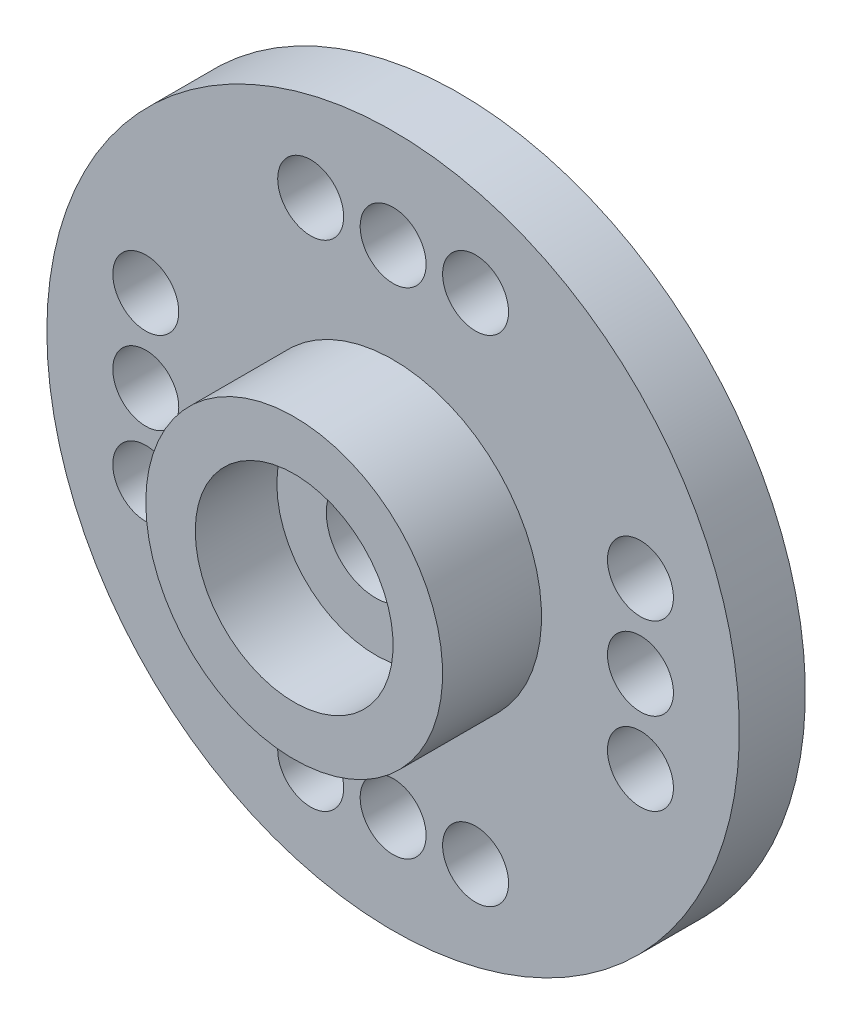
SolidWorks part; units mm, degrees
ref_plane "Alzado" through (0, 0, 0) normal (0, 0, 1) x (1, 0, 0)
ref_plane "Planta" through (0, 0, 0) normal (0, 1, 0) x (1, 0, 0)
ref_plane "Vista lateral" through (0, 0, 0) normal (1, 0, 0) x (0, 0, -1)
sketch "Croquis2" plane through (0, 0, 0) normal (1, 0, 0) x (0, 0, -1)
  line L0 (0, 0) -> (0, 1.5) construction
  line L1 (0, 1.5) -> (0, 3) construction
  line L2 (0, 3) -> (1.5, 3) construction
  line L3 (1.5, 3) -> (1.5, 3.5) construction
  line L4 (1.5, 3.5) -> (-0.5, 3.5) construction
  line L5 (-0.5, 3.5) -> (-0.5, 4.5) construction
  line L6 (-0.5, 4.5) -> (1, 4.5) construction
  line L7 (1, 4.5) -> (1, 10.5) construction
  line L8 (1, 10.5) -> (-1, 10.5) construction
  line L9 (-1, 10.5) -> (-1, 4.5) construction
  line L10 (-1, 4.5) -> (-4, 4.5) construction
  line L11 (-4, 4.5) -> (-4, 3) construction
  line L12 (-4, 3) -> (-1.5255, 3) construction
  line L13 (-1.5255, 3) -> (-1.5255, 1.5) construction
  line L14 (-1.5255, 1.5) -> (0, 1.5) construction
  line L15 (0, 1.5) -> (0, 3)
  line L16 (0, 3) -> (1.5, 3)
  line L17 (1.5, 3) -> (1.5, 3.5)
  line L18 (1.5, 3.5) -> (-0.5, 3.5)
  line L19 (-0.5, 3.5) -> (-0.5, 4.5)
  line L20 (-0.5, 4.5) -> (1, 4.5)
  line L21 (1, 4.5) -> (1, 10.5)
  line L22 (1, 10.5) -> (-1, 10.5)
  line L23 (-1, 10.5) -> (-1, 4.5)
  line L24 (-1, 4.5) -> (-4, 4.5)
  line L25 (-4, 4.5) -> (-4, 3)
  line L26 (-4, 3) -> (-1.5255, 3)
  line L27 (-1.5255, 3) -> (-1.5255, 1.5)
  line L28 (-1.5255, 1.5) -> (0, 1.5)
  line L29 (0, 0) -> (-7.3524, 0) construction
  dimension "D1" = 1.5
  dimension "D2" = 1.5
  dimension "D3" = 0.5
  dimension "D6" = 6
  dimension "D7" = 1
  dimension "D8" = 2
  dimension "D9" = 3
  dimension "D10" = 1.5
revolve "Revolución1" add sketch "Croquis2" angle 360 about L29
sketch "Croquis3" plane through (0, 0, -1) normal (0, 0, -1) x (-1, 0, 0)
  line L0 (7.5, 0) -> (7.5, 2.5) construction
  line L1 (7.5, 0) -> (7.5, -2.5) construction
  circle A0 centre (7.5, 2.5) radius 1
  circle A1 centre (0, 7.5) radius 1
  circle A2 centre (7.5, 0) radius 1
  circle A3 centre (-7.5, 0) radius 1
  circle A4 centre (0, -7.5) radius 1
  circle A5 centre (2.5, -7.5) radius 1
  circle A6 centre (-7.5, -2.5) radius 1
  circle A7 centre (-2.5, 7.5) radius 1
  circle A8 centre (7.5, -2.5) radius 1
  circle A9 centre (-2.5, -7.5) radius 1
  circle A10 centre (-7.5, 2.5) radius 1
  circle A11 centre (2.5, 7.5) radius 1
  point P20 (0, 0)
  point P27 (0, 0)
  dimension "D1" = 4
  dimension "D2" = 4
extrude "Cortar-Extruir1" cut sketch "Croquis3" against normal blind 3
